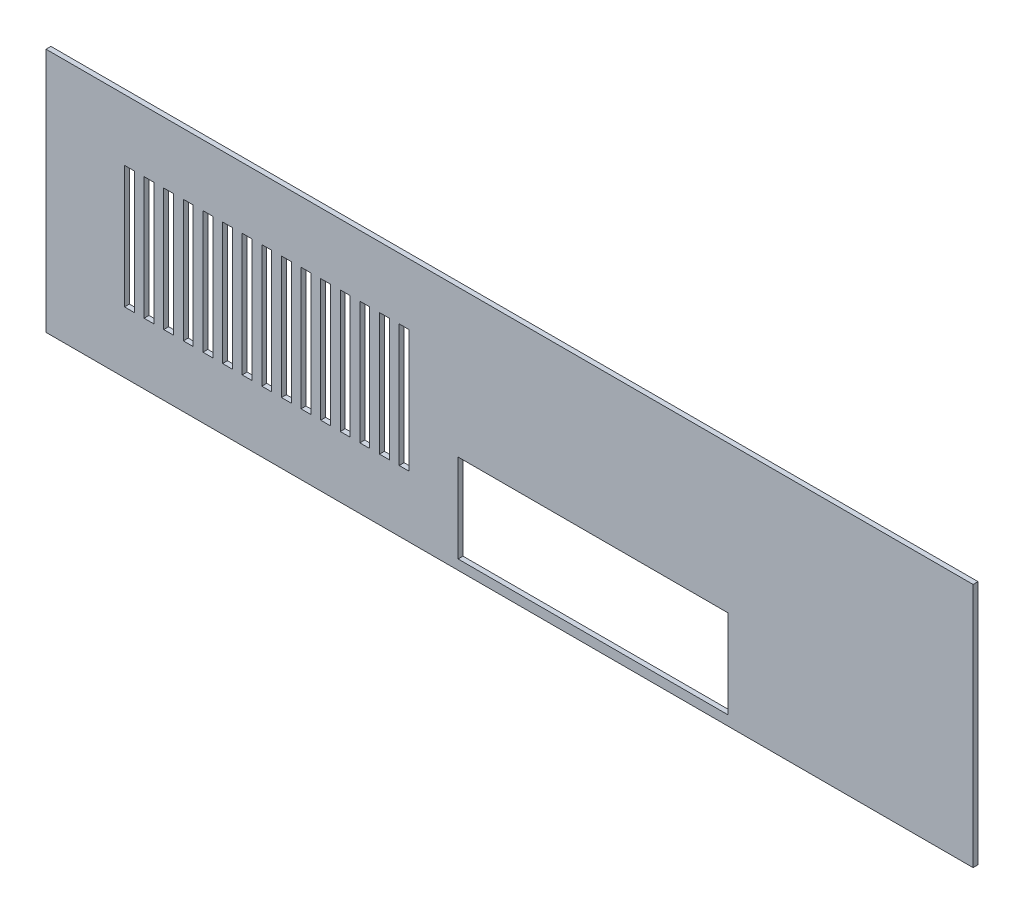
SolidWorks part; units mm, degrees
ref_plane "Front Plane" through (0, 0, 0) normal (0, 0, 1) x (1, 0, 0)
ref_plane "Top Plane" through (0, 0, 0) normal (0, 1, 0) x (1, 0, 0)
ref_plane "Right Plane" through (0, 0, 0) normal (1, 0, 0) x (0, 0, -1)
sketch "Sketch1" plane through (0, 0, 0) normal (0, 0, 1) x (1, 0, 0)
  line L1 (-61.6344, 41.198) -> (127.3656, 41.198)
  line L2 (-61.6344, 41.198) -> (-61.6344, -8.802)
  line L3 (-61.6344, -8.802) -> (127.3656, -8.802)
  line L4 (127.3656, 41.198) -> (127.3656, -8.802)
  dimension "D1" = 50
  dimension "D2" = 189
extrude "Boss-Extrude1" add sketch "Sketch1" along normal blind 1
sketch "Sketch2" plane through (0, 0, 1) normal (0, 0, 1) x (1, 0, 0)
  line L0 (-61.6344, -8.802) -> (127.3656, -8.802) construction
  line L1 (22.3656, 11.198) -> (77.3656, 11.198)
  line L2 (22.3656, 11.198) -> (22.3656, -6.802)
  line L3 (22.3656, -6.802) -> (77.3656, -6.802)
  line L4 (77.3656, 11.198) -> (77.3656, -6.802)
  line L5 (127.3656, -8.802) -> (127.3656, 41.198) construction
  dimension "D1" = 55
  dimension "D2" = 18
  dimension "D3" = 2
  dimension "D4" = 50
extrude "Cut-Extrude1" cut sketch "Sketch2" against normal through all
sketch "Sketch3" plane through (0, 0, 0) normal (0, 0, -1) x (-1, 0, 0)
  line L1 (-22.3656, 11.198) -> (-22.3656, -6.802) construction
  line L2 (-12.3656, 28.698) -> (-10.3656, 28.698)
  line L3 (-12.3656, 28.698) -> (-12.3656, 3.698)
  line L4 (-12.3656, 3.698) -> (-10.3656, 3.698)
  line L10 (-10.3656, 28.698) -> (-10.3656, 3.698)
  line L11 (61.6344, -8.802) -> (-127.3656, -8.802) construction
  line L12 (-8.3656, 28.698) -> (-6.3656, 28.698)
  line L13 (-8.3656, 28.698) -> (-8.3656, 3.698)
  line L14 (-8.3656, 3.698) -> (-6.3656, 3.698)
  line L15 (-6.3656, 28.698) -> (-6.3656, 3.698)
  line L16 (-4.3656, 28.698) -> (-2.3656, 28.698)
  line L17 (-4.3656, 28.698) -> (-4.3656, 3.698)
  line L18 (-4.3656, 3.698) -> (-2.3656, 3.698)
  line L19 (-2.3656, 28.698) -> (-2.3656, 3.698)
  line L20 (-0.3656, 28.698) -> (1.6344, 28.698)
  line L21 (-0.3656, 28.698) -> (-0.3656, 3.698)
  line L22 (-0.3656, 3.698) -> (1.6344, 3.698)
  line L23 (1.6344, 28.698) -> (1.6344, 3.698)
  line L24 (3.6344, 28.698) -> (5.6344, 28.698)
  line L25 (3.6344, 28.698) -> (3.6344, 3.698)
  line L26 (3.6344, 3.698) -> (5.6344, 3.698)
  line L27 (5.6344, 28.698) -> (5.6344, 3.698)
  line L28 (7.6344, 28.698) -> (9.6344, 28.698)
  line L29 (7.6344, 28.698) -> (7.6344, 3.698)
  line L30 (7.6344, 3.698) -> (9.6344, 3.698)
  line L31 (9.6344, 28.698) -> (9.6344, 3.698)
  line L32 (11.6344, 28.698) -> (13.6344, 28.698)
  line L33 (11.6344, 28.698) -> (11.6344, 3.698)
  line L34 (11.6344, 3.698) -> (13.6344, 3.698)
  line L35 (13.6344, 28.698) -> (13.6344, 3.698)
  line L36 (15.6344, 28.698) -> (17.6344, 28.698)
  line L37 (15.6344, 28.698) -> (15.6344, 3.698)
  line L38 (15.6344, 3.698) -> (17.6344, 3.698)
  line L39 (17.6344, 28.698) -> (17.6344, 3.698)
  line L40 (19.6344, 28.698) -> (21.6344, 28.698)
  line L41 (19.6344, 28.698) -> (19.6344, 3.698)
  line L42 (19.6344, 3.698) -> (21.6344, 3.698)
  line L43 (21.6344, 28.698) -> (21.6344, 3.698)
  line L44 (23.6344, 28.698) -> (25.6344, 28.698)
  line L45 (23.6344, 28.698) -> (23.6344, 3.698)
  line L46 (23.6344, 3.698) -> (25.6344, 3.698)
  line L47 (25.6344, 28.698) -> (25.6344, 3.698)
  line L48 (27.6344, 28.698) -> (29.6344, 28.698)
  line L49 (27.6344, 28.698) -> (27.6344, 3.698)
  line L50 (27.6344, 3.698) -> (29.6344, 3.698)
  line L51 (29.6344, 28.698) -> (29.6344, 3.698)
  line L52 (31.6344, 28.698) -> (33.6344, 28.698)
  line L53 (31.6344, 28.698) -> (31.6344, 3.698)
  line L54 (31.6344, 3.698) -> (33.6344, 3.698)
  line L55 (33.6344, 28.698) -> (33.6344, 3.698)
  line L56 (35.6344, 28.698) -> (37.6344, 28.698)
  line L57 (35.6344, 28.698) -> (35.6344, 3.698)
  line L58 (35.6344, 3.698) -> (37.6344, 3.698)
  line L59 (37.6344, 28.698) -> (37.6344, 3.698)
  line L60 (39.6344, 28.698) -> (41.6344, 28.698)
  line L61 (39.6344, 28.698) -> (39.6344, 3.698)
  line L62 (39.6344, 3.698) -> (41.6344, 3.698)
  line L63 (41.6344, 28.698) -> (41.6344, 3.698)
  line L64 (43.6344, 28.698) -> (45.6344, 28.698)
  line L65 (43.6344, 28.698) -> (43.6344, 3.698)
  line L66 (43.6344, 3.698) -> (45.6344, 3.698)
  line L67 (45.6344, 28.698) -> (45.6344, 3.698)
  dimension "D1" = 2
  dimension "D2" = 25
  dimension "D3" = 10
  dimension "D4" = 12.5
extrude "Cut-Extrude2" cut sketch "Sketch3" against normal through all
